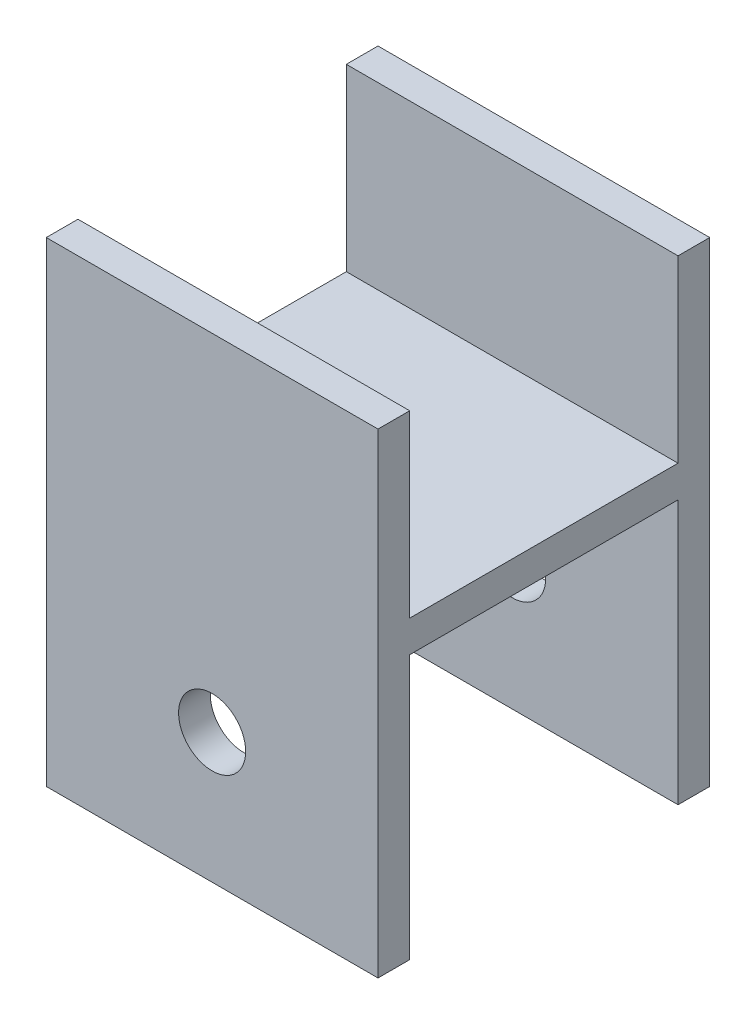
SolidWorks part; units mm, degrees
ref_plane "Front Plane" through (0, 0, 0) normal (0, 0, 1) x (1, 0, 0)
ref_plane "Top Plane" through (0, 0, 0) normal (0, 1, 0) x (1, 0, 0)
ref_plane "Right Plane" through (0, 0, 0) normal (1, 0, 0) x (0, 0, -1)
sketch "Sketch1" plane through (0, 0, 0) normal (1, 0, 0) x (0, 0, -1)
  line L15 (0, 0) -> (0, 45)
  line L16 (0, 45) -> (3, 45)
  line L17 (3, 45) -> (3, 28)
  line L18 (3, 28) -> (28.4, 28)
  line L19 (28.4, 28) -> (28.4, 45)
  line L20 (28.4, 45) -> (31.4, 45)
  line L21 (31.4, 45) -> (31.4, 0)
  line L22 (31.4, 0) -> (28.4, 0)
  line L23 (28.4, 0) -> (28.4, 25)
  line L24 (28.4, 25) -> (3, 25)
  line L25 (3, 25) -> (3, 0)
  line L26 (3, 0) -> (0, 0)
  dimension "D1" = 3
  dimension "D2" = 3
  dimension "D3" = 3
  dimension "D4" = 25.4
  dimension "D5" = 20
  dimension "D6" = 25
sketch "Sketch2" plane through (0, 0, 0) normal (0, 1, 0) x (-1, 0, 0)
  line L0 (0, 11) -> (0, -11) construction
  line L5 (11, 0) -> (-11, 0) construction
  line L10 (31.4, 0) -> (28.4, 0)
  line L11 (31.4, 0) -> (31.4, 31.4)
  line L12 (31.4, 31.4) -> (28.4, 31.4)
  line L13 (28.4, 0) -> (28.4, 31.4)
  line L15 (0, 31.4) -> (3, 31.4)
  line L16 (0, 31.4) -> (0, 0)
  line L17 (0, 0) -> (3, 0)
  line L18 (3, 31.4) -> (3, 0)
  dimension "D1" = 3
  dimension "D2" = 3
  dimension "D3" = 31.4
  dimension "D4" = 25.4
extrude "Boss-Extrude1" add sketch "Sketch1" along normal blind 31.4
hole_wizard "1/4 (0.25) Diameter Hole1" positions "Sketch3" profile "Sketch4" hole size "1/4" standard "ANSI Inch" end condition through all
sketch "Sketch3" plane through (0, 0, 0) normal (0, 0, 1) x (1, 0, 0)
  line L0 (31.4, 0) -> (0, 0) construction
  point P0 (15.7, 12.3)
  point P6 (15.7, 0)
  dimension "D1" = 12.7
sketch "Sketch4" plane through (15.7, 12.3, 0) normal (1, 0, 0) x (0, -1, 0)
  line L0 (0, 0) -> (0, 31.4)
  line L1 (0, 31.4) -> (3.175, 31.4)
  line L2 (3.175, 31.4) -> (3.175, 0)
  line L5 (3.175, 0) -> (0, 0)
  line L11 (0, -6.35) -> (0, 107.95) construction
  dimension "Thru Hole Dia." = 6.35
  dimension "Thru Hole Depth" = 31.4
